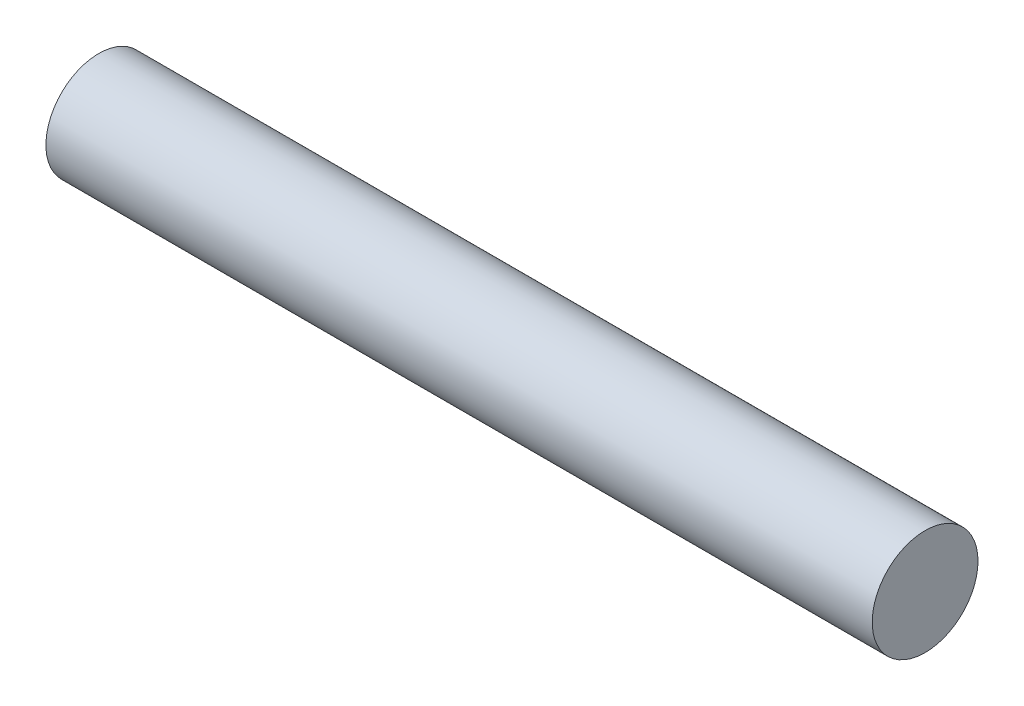
SolidWorks part; units mm, degrees
ref_plane "Front Plane" through (0, 0, 0) normal (0, 0, 1) x (1, 0, 0)
ref_plane "Top Plane" through (0, 0, 0) normal (0, 1, 0) x (1, 0, 0)
ref_plane "Right Plane" through (0, 0, 0) normal (1, 0, 0) x (0, 0, -1)
sketch "Sketch1" plane through (0, 0, 0) normal (1, 0, 0) x (0, 0, -1)
  circle A0 centre (0, 0) radius 8.128
  dimension "D1" = 16.256
extrude "Boss-Extrude1" add sketch "Sketch1" along normal blind 127
